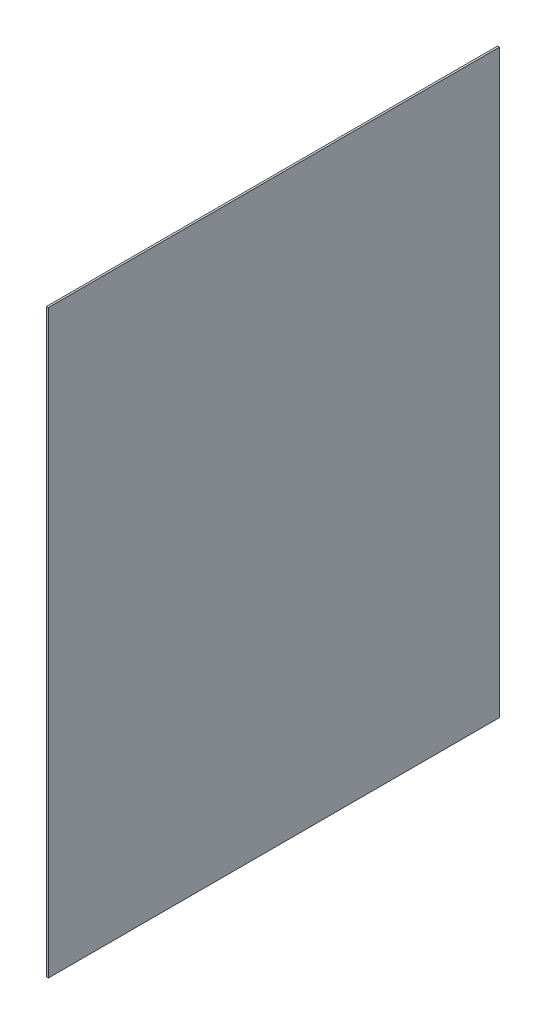
SolidWorks part; units mm, degrees
ref_plane "Front Plane" through (0, 0, 0) normal (0, 0, 1) x (1, 0, 0)
ref_plane "Top Plane" through (0, 0, 0) normal (0, 1, 0) x (1, 0, 0)
ref_plane "Right Plane" through (0, 0, 0) normal (1, 0, 0) x (0, 0, -1)
sketch "Croquis1" plane through (0, 0, 0) normal (1, 0, 0) x (0, 0, -1)
  line L1 (0, 0) -> (23.3, 0)
  line L2 (0, 0) -> (0, 30)
  line L3 (0, 30) -> (23.3, 30)
  line L4 (23.3, 0) -> (23.3, 30)
  dimension "D1" = 23.3
  dimension "D2" = 30
extrude "Saliente-Extruir1" add sketch "Croquis1" along normal blind 0.1
sketch "Croquis3"
